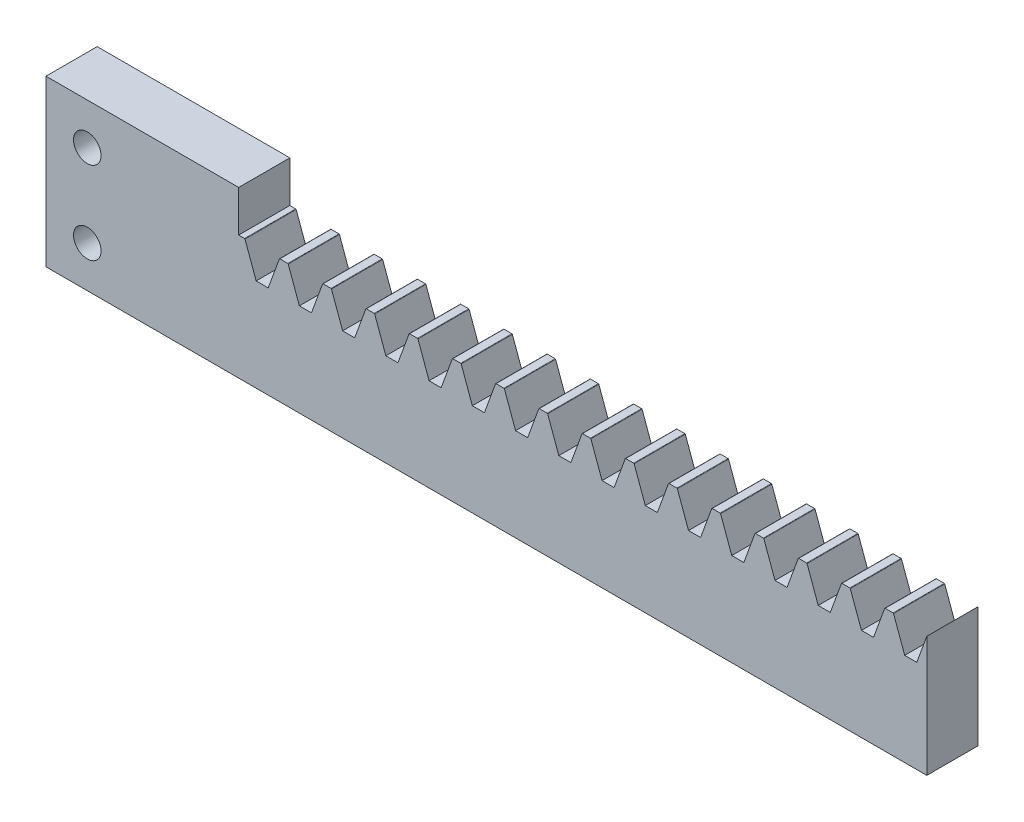
SolidWorks part; units mm, degrees
ref_plane "Plane1" through (0, 0, 0) normal (0, 0, 1) x (1, 0, 0)
ref_plane "Plane2" through (0, 0, 0) normal (0, 1, 0) x (1, 0, 0)
ref_plane "Plane3" through (0, 0, 0) normal (1, 0, 0) x (0, 0, -1)
sketch "HoldingSke" plane through (0, 0, 0) normal (0, 1, 0) x (1, 0, 0)
  line L0 (0, 0) -> (155.6602, -130.6144)
  line L1 (-15, 0) -> (100, 0) construction
  line L2 (0, 0) -> (-2.1039, 2.3779)
  line L3 (0, 0) -> (-11.863, 4.5341)
  line L4 (0, 0) -> (8.0072, 3.2351)
  line L5 (0, 0) -> (-23.7986, -8.8762)
  line L6 (0, 0) -> (-10.5278, -7.1032)
  line L9 (-71.009, 38.7566) -> (119.9366, 108.2551)
  line L10 (-76.2, 71.12) -> (-50.8, 71.12)
  line L11 (0, 0) -> (-11.811, 0)
  line L12 (-76.2, 101.6) -> (-76.0857, 101.6)
  line L13 (24.9733, 27.94) -> (52.9518, 28.4284)
  line L14 (24.9733, 27.94) -> (24.9746, 27.94)
  line L15 (24.9733, 27.94) -> (100.4006, 29.5858)
  circle A0 centre (0, 0) radius 19.05
  circle A1 centre (0, 0) radius 12.7
  circle A2 centre (0, 0) radius 12.7
  dimension "MPH" = 25.4
  dimension "Diameter" = 38.1
  dimension "Num_teeth" = 22
  dimension "Pitch" = 203.2
  dimension "Width" = 11.811
  dimension "Show_teeth" = 400
  dimension "Thickness" = 12.7
  dimension "Ap" = 20
  dimension "Pitch_height" = 25.4
  dimension "Backlash" = 0.1143
  dimension "Addendum_fac" = 1
  dimension "Dedendum_fac" = 1.25
  dimension "Clearance_fac" = 0.25
  dimension "Dedendum_add" = 0.0013
  dimension "Length" = 203.2
sketch "BlankSke" plane through (0, 0, 0) normal (0, 0, 1) x (1, 0, 0)
  line L1 (0, 0) -> (203.2, 0)
  line L2 (0, 0) -> (0, 28.575)
  line L3 (0, 28.575) -> (203.2, 28.575)
  line L4 (203.2, 0) -> (203.2, 28.575)
  dimension "Length" = 203.2
  dimension "Blank_height" = 28.575
extrude "Blank" add sketch "BlankSke" against normal blind 11.811
sketch "TooCutSkeIll" plane through (0, 0, 0) normal (0, 0, 1) x (1, 0, 0)
  line L0 (-3.9617, 28.4914) -> (-1.5824, 21.9544)
  line L1 (-0.8354, 21.4312) -> (0.8354, 21.4312)
  line L2 (1.5824, 21.9544) -> (3.9617, 28.4914)
  line L3 (203.2, 28.575) -> (0, 28.575) construction
  line L4 (0, 0) -> (0, 64.897) construction
  line L5 (-13.208, 25.4) -> (12.954, 25.4) construction
  line L6 (0, 0) -> (203.2, 0) construction
  line L7 (2.8365, 25.4) -> (2.8365, 48.7463) construction
  line L8 (-2.8365, 25.4) -> (-2.8365, 48.7463) construction
  line L9 (4.0811, 28.575) -> (4.0811, 28.6004)
  line L10 (-4.0811, 28.575) -> (-4.0811, 28.6004)
  line L11 (-4.0811, 28.6004) -> (4.0811, 28.6004)
  arc A0 (0.8354, 21.4312) -> (1.5824, 21.9544) centre (0.8354, 22.2263) ccw
  arc A1 (-1.5824, 21.9544) -> (-0.8354, 21.4312) centre (-0.8354, 22.2263) ccw
  arc A2 (4.0811, 28.575) -> (3.9617, 28.4914) centre (4.0811, 28.448) ccw
  arc A3 (-3.9617, 28.4914) -> (-4.0811, 28.575) centre (-4.0811, 28.448) ccw
  dimension "Root_fillet" = 0.795
  dimension "Break_rad" = 0.127
  dimension "Pitch_height" = 25.4
  dimension "Gap_width" = 5.6731
  dimension "Dedendum" = 3.9688
  dimension "Addendum_plus" = 3.2004
  dimension "Pressure_angle" = 20
extrude "ToothCutIll" cut sketch "TooCutSkeIll" against normal through all
sketch "TooCutSkeSim" plane through (0, 0, 0) normal (0, 0, 1) x (1, 0, 0)
  line L0 (1.392, 21.4312) -> (-1.392, 21.4312)
  line L1 (4.0014, 28.6004) -> (1.392, 21.4312)
  line L2 (0, 17.4625) -> (0, 53.467) construction
  line L3 (4.0014, 28.6004) -> (-4.0014, 28.6004)
  line L6 (-4.0014, 28.6004) -> (-1.392, 21.4312)
  line L9 (-2.8365, 25.4) -> (2.8365, 25.4) construction
  line L10 (0, 0) -> (203.2, 0) construction
  line L11 (2.8365, 25.4) -> (2.8365, 53.467) construction
  line L12 (-2.8365, 25.4) -> (-2.8365, 53.467) construction
  dimension "Pitch_height" = 25.4
  dimension "Pressure_angle" = 20
  dimension "Gap_width" = 5.6731
  dimension "Dedendum" = 3.9688
  dimension "Addendum_plus" = 3.2004
extrude "ToothCutSim" cut sketch "TooCutSkeSim" against normal through all
pattern_linear "TeethCuts" count 22 spacing 9.9746 along (1, 0, 0) of "ToothCutIll", "ToothCutSim"
sketch "Sketch1" plane through (0, 0, 0) normal (0, 0, 1) x (1, 0, 0)
  line L1 (0, 0) -> (44.45, 0)
  line L2 (0, 0) -> (0, 38.1)
  line L3 (0, 38.1) -> (44.45, 38.1)
  line L4 (44.45, 0) -> (44.45, 38.1)
  dimension "D1" = 38.1
  dimension "D2" = 44.45
extrude "Boss-Extrude1" add sketch "Sketch1" against normal blind 11.811
sketch "Sketch2" plane through (0, 0, 0) normal (0, 0, 1) x (1, 0, 0)
  line L2 (0, 19.05) -> (28.6372, 19.05) construction
  line L3 (0, 38.1) -> (0, 0) construction
  circle A0 centre (9.525, 28.575) radius 3.175
  circle A1 centre (9.525, 9.525) radius 3.175
  dimension "D1" = 6.35
  dimension "D4" = 9.525
  dimension "D2" = 19.05
  dimension "D3" = 19.05
extrude "Cut-Extrude1" cut sketch "Sketch2" against normal through all
equation "' \"Pitch@HoldingSke\" = 4"
equation "' \"Num_teeth@HoldingSke\" = 12"
equation "' \"Ap@HoldingSke\" =  20"
equation "' \"Width@HoldingSke\" = 0.25"
equation "' \"Show_teeth@HoldingSke\" = 500"
equation "' \"Backlash@HoldingSke\" = 0.009"
equation "' \"Addendum_fac@HoldingSke\" = 1.0"
equation "' \"Dedendum_fac@HoldingSke\" = 1.25"
equation "' \"Dedendum_add@HoldingSke\" = 0.00005"
equation "' \"Clearance_fac@HoldingSke\" = 0.25"
equation "' \"Pitch_height@HoldingSke\" = 1"
equation "' \"Length@HoldingSke\" = 4.71"
equation "\"MPH@HoldingSke\" = \"Dedendum_fac@HoldingSke\" / \"Pitch@HoldingSke\" + 2 * \"Dedendum_add@HoldingSke\" + 0.002"
equation "\"MPH@HoldingSke\" = ((sgn( \"MPH@HoldingSke\" - \"Pitch_height@HoldingSke\")+1)*( \"MPH@HoldingSke\" - \"Pitch_height@HoldingSke\"))/2 + \"Pitch_height@HoldingSke\""
equation "\"Blank_height@BlankSke\" = \"Pitch_height@HoldingSke\" + \"Addendum_fac@HoldingSke\"  / \"Pitch@HoldingSke\" "
equation "\"Length@BlankSke\" =  \"Length@HoldingSke\""
equation "\"Face_width@Blank\" = \"Width@HoldingSke\""
equation "\"Pressure_angle@TooCutSkeIll\" = \"Ap@HoldingSke\""
equation "\"Addendum_plus@TooCutSkeIll\" =  \"Addendum_fac@HoldingSke\"  / \"Pitch@HoldingSke\" + 0.001"
equation "\"Dedendum@TooCutSkeIll\" = \"Dedendum_fac@HoldingSke\"  / \"Pitch@HoldingSke\""
equation "\"Pitch_height@TooCutSkeIll\" =  \"MPH@HoldingSke\""
equation "\"Gap_width@TooCutSkeIll\" = 3.14159265 / 2 / \"Pitch@HoldingSke\" + 6 * \"Backlash@HoldingSke\""
equation "\"Pressure_angle@TooCutSkeSim\" = \"Ap@HoldingSke\""
equation "\"Addendum_plus@TooCutSkeSim\" =  \"Addendum_fac@HoldingSke\"  / \"Pitch@HoldingSke\" + 0.001"
equation "\"Dedendum@TooCutSkeSim\" = \"Dedendum_fac@HoldingSke\"  / \"Pitch@HoldingSke\""
equation "\"Pitch_height@TooCutSkeSim\" =  \"MPH@HoldingSke\""
equation "\"Gap_width@TooCutSkeSim\" = 3.14159265 / 2 / \"Pitch@HoldingSke\" + 6 * \"Backlash@HoldingSke\""
equation "\"Root_fillet@TooCutSkeIll\" = \"Clearance_fac@HoldingSke\" / \"Pitch@HoldingSke\" + \"Dedendum_add@HoldingSke\""
equation "\"Break_rad@TooCutSkeIll\" = 0.02 / \"Pitch@HoldingSke\" * 2"
equation "\"Linear_pitch@TeethCuts\" = 3.14159265 / \"Pitch@HoldingSke\""
equation "\"Num_teeth@HoldingSke\" = int( ( \"Length@HoldingSke\" + 0 ) / (3.14159265 / \"Pitch@HoldingSke\")) + 0.9999  + 1"
equation " \"Num_teeth@TeethCuts\" = int( \"Show_teeth@HoldingSke\" ) + 1"
equation " \"Num_teeth@TeethCuts\" = ((sgn( \"Num_teeth@TeethCuts\" - \"Num_teeth@HoldingSke\" )-1)*( \"Num_teeth@TeethCuts\" - \"Num_teeth@HoldingSke\" ))/-2+ \"Num_teeth@HoldingSke\""
equation " \"Num_teeth@TeethCuts\" = ((sgn( \"Num_teeth@TeethCuts\" - 2.0)+1)*( \"Num_teeth@TeethCuts\" - 2.0))/2 +2.0"
